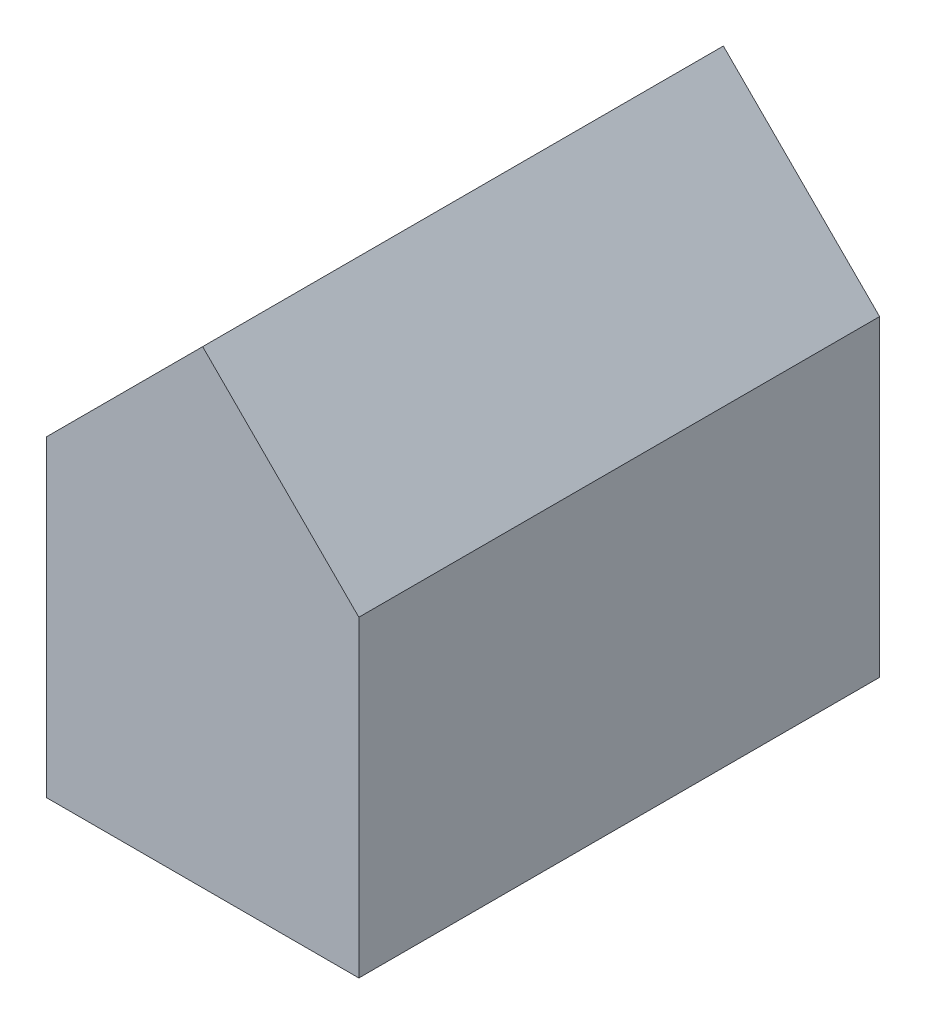
SolidWorks part; units mm, degrees
ref_plane "Front Plane" through (0, 0, 0) normal (0, 0, 1) x (1, 0, 0)
ref_plane "Top Plane" through (0, 0, 0) normal (0, 1, 0) x (1, 0, 0)
ref_plane "Right Plane" through (0, 0, 0) normal (1, 0, 0) x (0, 0, -1)
sketch "Sketch1" plane through (0, 0, 0) normal (0, 0, 1) x (1, 0, 0)
  line L0 (-27.7113, 16.1031) -> (-24.7113, 19.1031)
  line L2 (-27.7113, 16.1031) -> (-27.7113, 10.1031)
  line L3 (-27.7113, 10.1031) -> (-21.7113, 10.1031)
  line L4 (-21.7113, 16.1031) -> (-21.7113, 10.1031)
  line L5 (-24.7113, 19.1031) -> (-21.7113, 16.1031)
  dimension "D4" = 9
extrude "Boss-Extrude1" add sketch "Sketch1" along normal blind 10 contours L2 L3 L4 L5 L0
